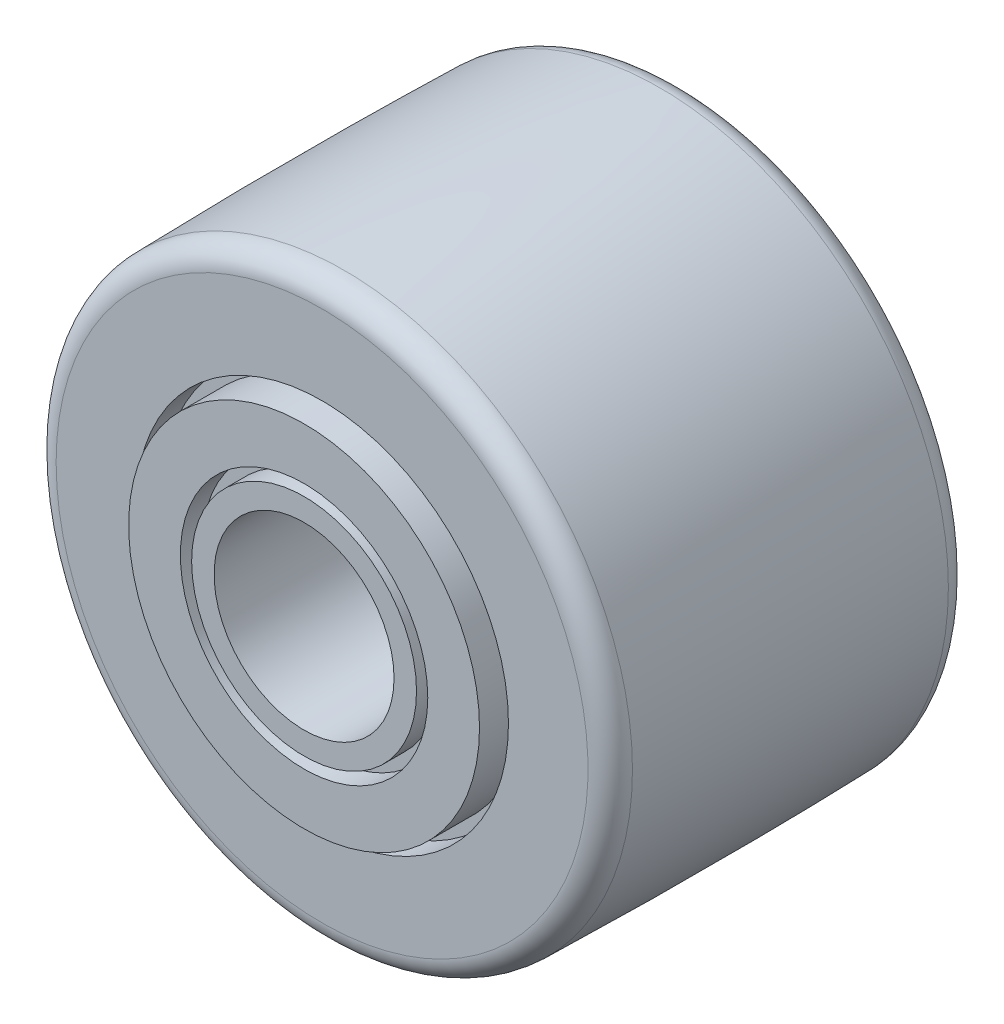
SolidWorks part; units mm, degrees
ref_plane "Front" through (0, 0, 0) normal (0, 0, 1) x (1, 0, 0)
ref_plane "Top" through (0, 0, 0) normal (0, 1, 0) x (1, 0, 0)
ref_plane "Right" through (0, 0, 0) normal (1, 0, 0) x (0, 0, -1)
sketch "Sketch1" plane through (0, 0, 0) normal (1, 0, 0) x (0, 0, -1)
  line L0 (0, 7.7391) -> (0.7938, 7.7391)
  line L1 (17.4625, 7.7391) -> (17.4625, -7.7391) construction
  line L2 (0.7937, 12.7) -> (0.7938, 7.7391)
  line L3 (0.7937, 12.7) -> (16.6687, 12.7) construction
  line L4 (16.6687, 12.7) -> (16.6687, 7.7391)
  line L5 (0, 7.7391) -> (0, -7.7391) construction
  line L6 (16.6687, 7.7391) -> (17.4625, 7.7391)
  line L7 (0, 0) -> (17.4625, 0)
  line L8 (16.6687, -7.7391) -> (17.4625, -7.7391) construction
  line L9 (16.6687, -12.7) -> (16.6687, -7.7391) construction
  line L10 (0.7938, -12.7) -> (16.6687, -12.7) construction
  line L11 (0.7938, -12.7) -> (0.7938, -7.7391) construction
  line L12 (0, -7.7391) -> (0.7938, -7.7391) construction
  line L13 (17.4625, 7.7391) -> (17.4625, 0)
  line L14 (0, 7.7391) -> (0, 0)
  line L15 (8.7312, 12.8034) -> (8.7312, -12.7) construction
  arc A0 (0.7937, 12.7) -> (16.6687, 12.7) centre (8.7312, -291.9966) cw
  point P3 (0.9922, 0)
  point P15 (1.9844, 0)
  dimension "D1" = 0.9922
  dimension "D2" = 1.9844
revolve "Revolve1" add sketch "Sketch1" angle 360 mid plane about L7
sketch "Sketch2" plane through (0, 0, 0) normal (0, 0, 1) x (1, 0, 0)
  circle A0 centre (0, 0) radius 3.9688
extrude "Cut-Extrude1" cut sketch "Sketch2" against normal through all
sketch "Sketch3" plane through (0, 0, 0) normal (0, 0, 1) x (1, 0, 0)
  circle A0 centre (0, 0) radius 4.9609
  circle A1 centre (0, 0) radius 5.457
  circle A2 centre (0, 0) radius 3.9688 construction
  dimension "D1" = 0.9922
  dimension "D2" = 0.4961
extrude "Cut-Extrude2" cut sketch "Sketch3" against normal up to vertex (0.9922 mm away) up to point (0, 0, -0.9922)
sketch "Sketch4" plane through (0, 0, -0.7938) normal (0, 0, 1) x (1, 0, 0)
  circle A1 centre (0, 0) radius 8.2228
  circle A2 centre (0, 0) radius 7.7391
  circle A3 centre (0, 0) radius 7.7391
  dimension "D2" = 0.4837
extrude "Cut-Extrude3" cut sketch "Sketch4" against normal up to vertex (1.1906 mm away) up to point (0, 0, -1.9844)
fillet "Fillet1" radius 0.9922 2 edges at (12.7, 0, -16.6687) (12.7, 0, -0.7937)
ref_plane "Plane1" through (0, 0, -8.7312) normal (0, 0, 1) x (1, 0, 0)
mirror "Mirror1" about plane through (0, 0, -8.7312) normal (0, 0, 1) of "Cut-Extrude3", "Cut-Extrude2"
equation "\"D1@Sketch3\" = \"F Bore ID@Sketch2\" * .125"
equation "\"D2@Sketch3\" = \"D1@Sketch3\" * .5"
equation "\"D1@Sketch1\" = \"B Roller Width@Sketch1\" * .0625"
equation "\"D2@Sketch4\" = \"H Min Clamping Dia@Sketch1\" * .03125"
equation "\"D2@Sketch1\" = \"B Roller Width@Sketch1\"*.125"
equation "\"D1@Fillet1\" = \"B Roller Width@Sketch1\" * .0625"
